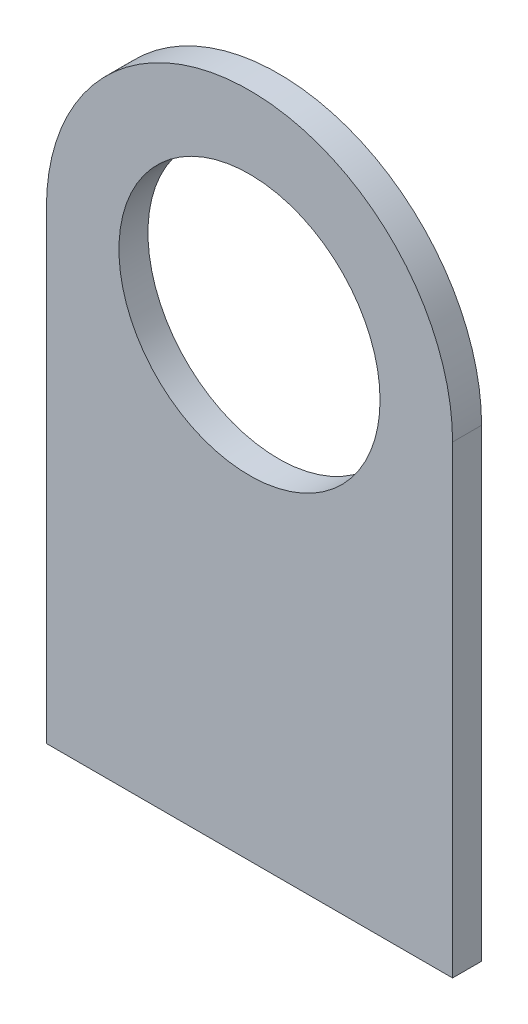
SolidWorks part; units mm, degrees
ref_plane "Front Plane" through (0, 0, 0) normal (0, 0, 1) x (1, 0, 0)
ref_plane "Top Plane" through (0, 0, 0) normal (0, 1, 0) x (1, 0, 0)
ref_plane "Right Plane" through (0, 0, 0) normal (1, 0, 0) x (0, 0, -1)
sketch "Sketch1" plane through (0, 0, 0) normal (0, 0, 1) x (1, 0, 0)
  line L0 (-22.225, 0) -> (-22.225, -50.8)
  line L1 (-22.225, -50.8) -> (22.225, -50.8)
  line L2 (22.225, -50.8) -> (22.225, 0)
  circle A0 centre (0, 0) radius 14.2875
  arc A1 (22.225, 0) -> (-22.225, 0) centre (0, 0) ccw
  dimension "D1" = 28.575
  dimension "D3" = 50.8
extrude "Boss-Extrude1" add sketch "Sketch1" along normal blind 3.175
